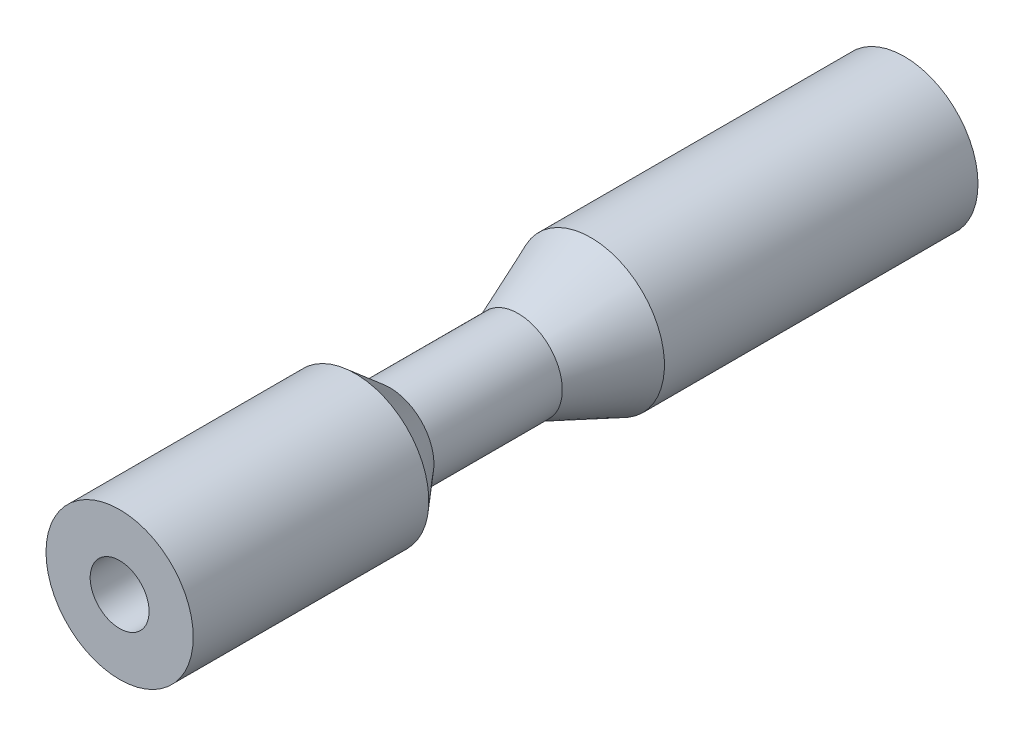
SolidWorks part; units mm, degrees
ref_plane "Front Plane" through (0, 0, 0) normal (0, 0, 1) x (1, 0, 0)
ref_plane "Top Plane" through (0, 0, 0) normal (0, 1, 0) x (1, 0, 0)
ref_plane "Right Plane" through (0, 0, 0) normal (1, 0, 0) x (0, 0, -1)
sketch "Sketch1" plane through (0, 0, 0) normal (0, 0, 1) x (1, 0, 0)
  circle A0 centre (0, 0) radius 2.5
  dimension "D1" = 5
extrude "Boss-Extrude1" add sketch "Sketch1" along normal blind 27
sketch "Sketch3" plane through (0, 0, 0) normal (0, 1, 0) x (1, 0, 0)
  line L0 (2.5, -11) -> (1.5, -13.4678)
  line L1 (3.1382, -11) -> (2.5, -11)
  line L2 (3.1382, -11) -> (3.1382, -19)
  line L3 (3.1382, -19) -> (2.5, -19)
  line L4 (1.5, -13.4678) -> (1.5, -17.8277)
  line L5 (2.5, -27) -> (2.5, 0) construction
  line L6 (2.5, -19) -> (1.5, -17.8277)
  line L7 (0, 0) -> (0, -16.2401) construction
  line L8 (2.5, 0) -> (-2.5, 0) construction
  dimension "D1" = 1.5
  dimension "D2" = 11
  dimension "D3" = 8
revolve "Cut-Revolve1" cut sketch "Sketch3" angle 360 about L7
chamfer "Chamfer1" distance 2 angle 10 1 edges at (2.5, 0, 0)
hole_wizard "Ø2.0 (2) Diameter Hole1" positions "Sketch5" profile "Sketch4" hole size "Ø2.0" standard "Ansi Metric"
sketch "Sketch5" plane through (0, 0, 27) normal (0, 0, 1) x (1, 0, 0)
  point P0 (0, 0)
sketch "Sketch4" plane through (0, 0, 27) normal (1, 0, 0) x (0, -1, 0)
  line L0 (0, 0) -> (0, 26.6009)
  line L1 (0, 26.6009) -> (1, 26)
  line L2 (1, 26) -> (1, 0)
  line L5 (1, 0) -> (0, 0)
  line L10 (0, 26.6009) -> (-1, 26) construction
  line L11 (0, -6.35) -> (0, 107.95) construction
  dimension "Hole Dia." = 2
  dimension "Hole Depth" = 26
  dimension "Drill Angle" = 118
sketch "Sketch6" plane through (0, 0, 0) normal (0, 0, -1) x (-1, 0, 0)
  circle A0 centre (0, 0) radius 0.25
  dimension "D1" = 0.5
extrude "Cut-Extrude1" cut sketch "Sketch6" against normal up to next
